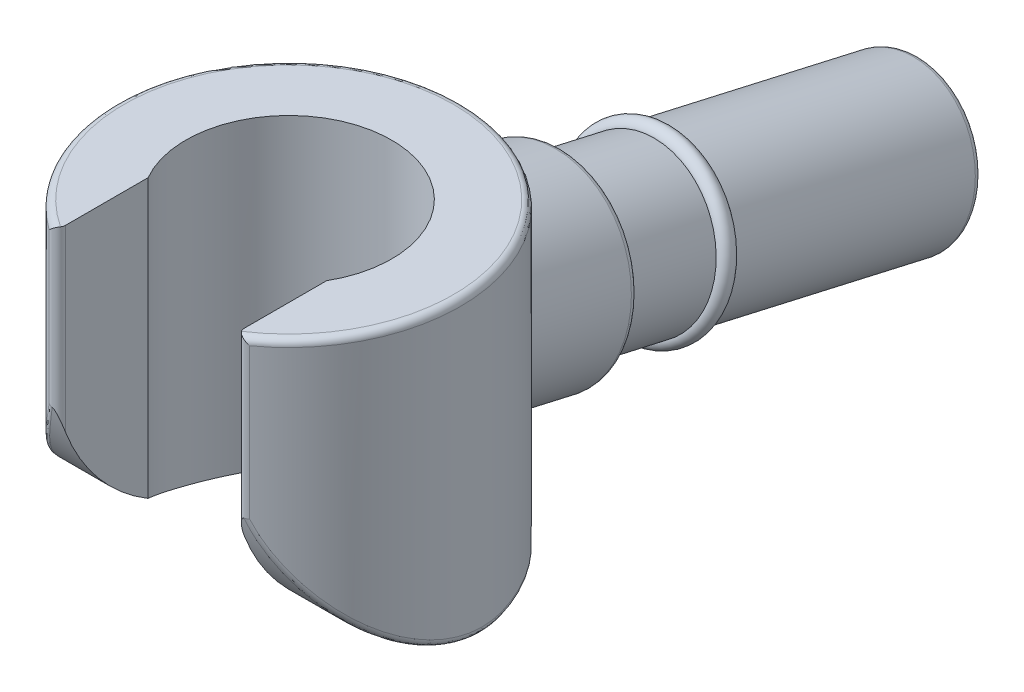
SolidWorks part; units mm, degrees
ref_plane "Front Plane" through (0, 0, 0) normal (0, 0, 1) x (1, 0, 0)
ref_plane "Top Plane" through (0, 0, 0) normal (0, 1, 0) x (1, 0, 0)
ref_plane "Right Plane" through (0, 0, 0) normal (1, 0, 0) x (0, 0, -1)
sketch "Sketch2" plane through (0, 0, 0) normal (0, 1, 0) x (1, 0, 0)
  line L2 (-1.3, -2.1354) -> (-1.3, -0.7483)
  line L4 (1.3, -2.1354) -> (1.3, -0.7483)
  arc A0 (1.3, -0.7483) -> (-1.3, -0.7483) centre (0, 0) ccw
  arc A1 (1.3, -2.1354) -> (-1.3, -2.1354) centre (0, 0) ccw
  point P4 (0, -2.5)
  dimension "D1" = 5
  dimension "D2" = 3
  dimension "D3" = 2.6
  dimension "D4" = 1.3
extrude "Hand" add sketch "Sketch2" along normal blind 4.45
sketch "Sketch3" plane through (0, 0, 0) normal (1, 0, 0) x (0, 0, -1)
  line L0 (-2.1354, 2.85) -> (-2.1354, 0)
  line L1 (-2.1354, 4.45) -> (-2.1354, 0) construction
  line L2 (-2.1354, 0) -> (0.66, 0)
  line L3 (-2.1354, 0) -> (2.5, 0) construction
  arc A0 (-2.1354, 2.85) -> (0.66, 0) centre (0.7151, 2.85) ccw
  dimension "D1" = 1.6
  dimension "D2" = 1.84
extrude "Hand Curve" cut sketch "Sketch3" against normal through all both and the other way through all
sketch "Sketch4" plane through (0, 0, 0) normal (1, 0, 0) x (0, 0, -1)
  line L0 (2.5, 2.0528) -> (8.9447, 0.5839) construction
  line L1 (2.5, 0) -> (2.5, 4.45) construction
  dimension "D1" = 77.16
  dimension "D2" = 6.61
ref_plane "Plane1" through (0, 0.5839, -8.9447) normal (0, -0.2222, -0.975) x (-1, 0, 0)
sketch "Sketch5" plane through (0, 0.5839, -8.9447) normal (0, -0.2222, -0.975) x (-1, 0, 0)
  circle A0 centre (0, 0) radius 1.125
  dimension "D1" = 2.25
extrude "Wrist" add sketch "Sketch5" against normal up to next
sketch "Sketch6" plane through (0, -1.9092, -8.3765) normal (0, -0.2222, -0.975) x (-1, 0, 0)
  circle A0 centre (0, 2.5571) radius 1.375
  circle A1 centre (0, 2.5571) radius 1.125 construction
  dimension "D1" = 2.75
extrude "Wrist Outer" add sketch "Sketch6" against normal up to next from offset 5.4 offset against normal yes
sketch "Sketch7" plane through (0, 0, 0) normal (1, 0, 0) x (0, 0, -1)
  line L0 (3.4297, 0.6871) -> (8.6947, -0.513) construction
  circle A0 centre (4.9447, 0.3417) radius 0.125
  dimension "D1" = 0.25
  dimension "D2" = 4
revolve "Wrist Ring" add sketch "Sketch7" angle 360 about L0
fillet "Fillet1" radius 0.1 10 edges at (-1.3, 3.65, 2.1354) (1.3, 3.65, 2.1354) (-2.1481, 0.8131, 1.279) (2.2123, 0.7068, 1.1643) (0, 0, -2.5) (0, 4.45, -2.5) (-0.0445, 0.6434, -2.4996) (0, 2.8808, -3.9298) (0, 3.1245, -3.9853) (0, 1.6808, -9.1947)
